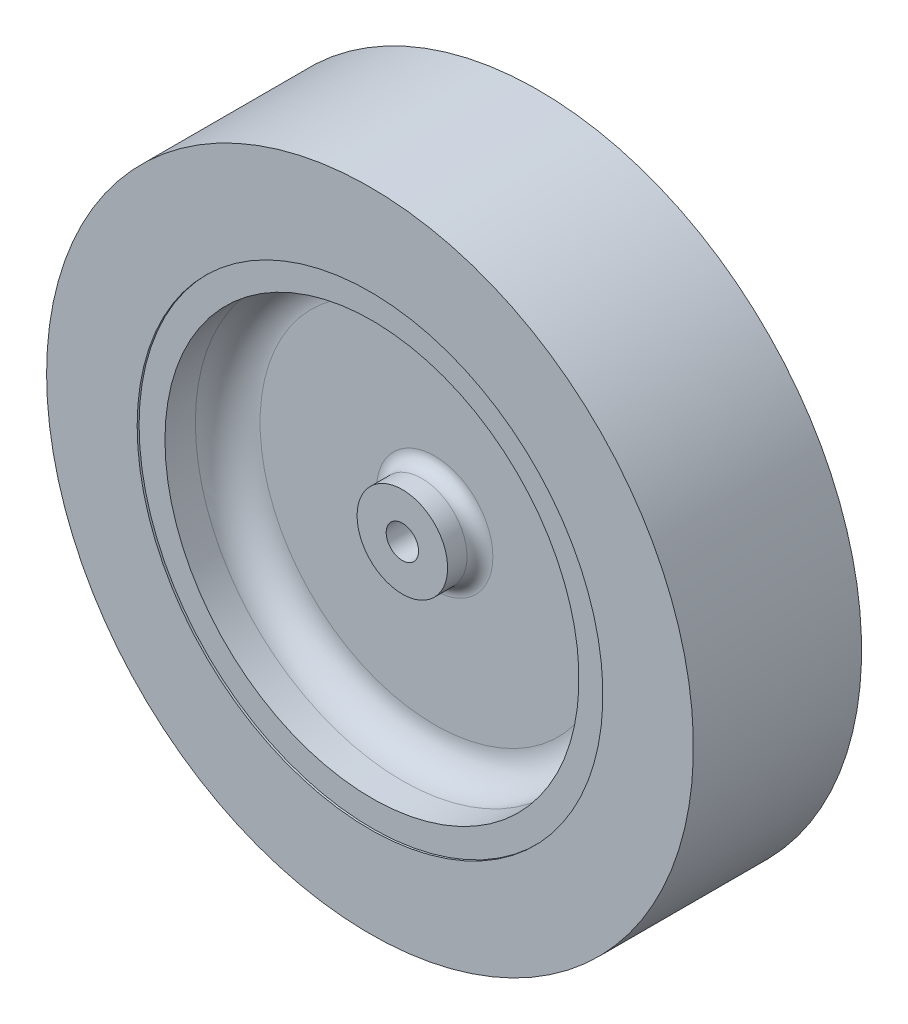
SolidWorks part; units mm, degrees
ref_plane "Front Plane" through (0, 0, 0) normal (0, 0, 1) x (1, 0, 0)
ref_plane "Top Plane" through (0, 0, 0) normal (0, 1, 0) x (1, 0, 0)
ref_plane "Right Plane" through (0, 0, 0) normal (1, 0, 0) x (0, 0, -1)
sketch "Sketch1" plane through (0, 0, 0) normal (0, 0, 1) x (1, 0, 0)
  circle A0 centre (0, 0) radius 42.7371 construction
sketch "Sketch2" plane through (0, 0, 0) normal (1, 0, 0) x (0, 0, -1)
  line L0 (-8, 2.5) -> (8, 2.5)
  line L1 (0, 0) -> (0, 50) construction
  line L2 (13, 50) -> (-13, 50)
  line L3 (-13, 50) -> (-13, 36)
  line L6 (-13, 36) -> (-12.7, 36)
  line L7 (-12.7, 36) -> (-12.7, 32)
  line L8 (-12.7, 32) -> (-3, 32)
  line L9 (-3, 32) -> (-3, 7)
  line L10 (-3, 7) -> (-8, 7)
  line L11 (-8, 7) -> (-8, 2.5)
  line L12 (8, 7) -> (8, 2.5)
  line L13 (3, 7) -> (8, 7)
  line L14 (3, 32) -> (3, 7)
  line L15 (12.7, 32) -> (3, 32)
  line L16 (12.7, 36) -> (12.7, 32)
  line L17 (13, 36) -> (12.7, 36)
  line L18 (13, 50) -> (13, 36)
  line L19 (5.5202, 0) -> (-7.9181, 0) construction
  point P16 (0, 2.5)
  dimension "D1" = 2.5
  dimension "D2" = 50
  dimension "D3" = 14
  dimension "D4" = 0.3
  dimension "D5" = 4
  dimension "D6" = 25
  dimension "D7" = 13
  dimension "D8" = 5
  dimension "D9" = 6
revolve "Revolve2" add sketch "Sketch2" angle 360 about L19
fillet "Fillet1" radius 5 1 edges at (-32, 0, -3)
fillet "Fillet2" radius 2 1 edges at (-7, 0, -3)
fillet "Fillet3" radius 5 1 edges at (-32, 0, 3)
fillet "Fillet4" radius 2 1 edges at (-7, 0, 3)
ref_plane "Plane1" through (50, 0, 0) normal (1, 0, 0) x (0, 0, -1)
